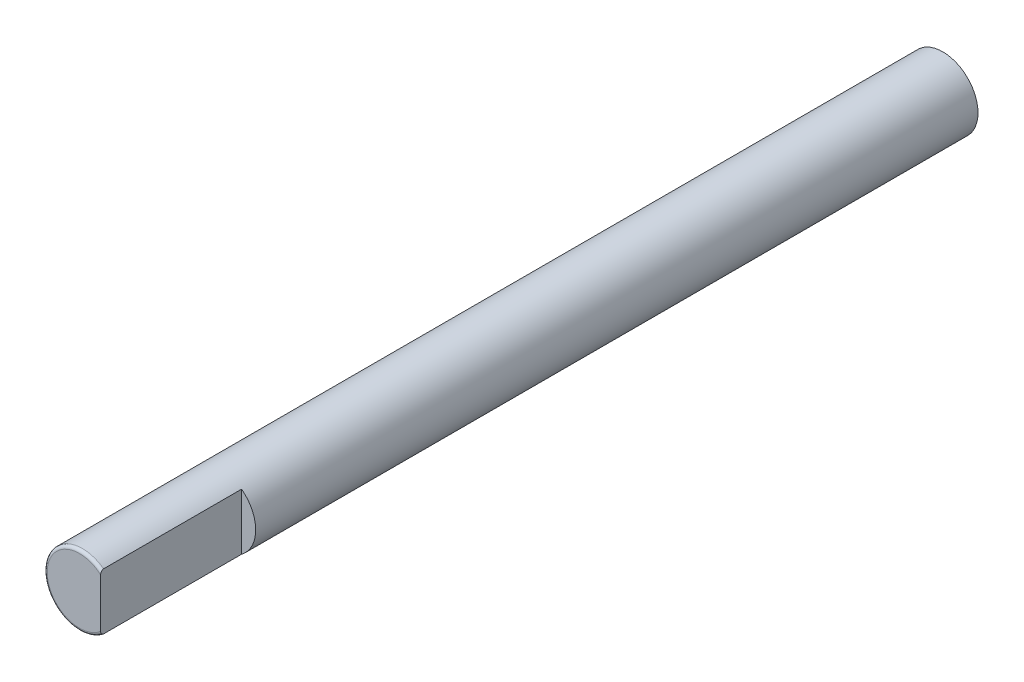
SolidWorks part; units mm, degrees
material "Acero aleado"
ref_plane "Alzado" through (0, 0, 0) normal (0, 0, 1) x (1, 0, 0)
ref_plane "Planta" through (0, 0, 0) normal (0, 1, 0) x (1, 0, 0)
ref_plane "Vista lateral" through (0, 0, 0) normal (1, 0, 0) x (0, 0, -1)
sketch "Croquis1" plane through (0, 0, 0) normal (0, 0, 1) x (1, 0, 0)
  circle A0 centre (0, 0) radius 3
  dimension "D1" = 6
extrude "Saliente-Extruir1" add sketch "Croquis1" along normal blind 73.5
sketch "Croquis2" plane through (0, 0, 73.5) normal (0, 0, 1) x (1, 0, 0)
  circle A0 centre (0, 0) radius 1
  dimension "D1" = 2
fillet "Redondeo1" radius 0.25 1 edges at (3, 0, 73.5)
sketch "Sketch1" plane through (0, 0, 73.5) normal (0, 0, 1) x (1, 0, 0)
  line L1 (1.8, 6.3205) -> (4.8651, 6.3205)
  line L2 (1.8, 6.3205) -> (1.8, -3.6795)
  line L3 (1.8, -3.6795) -> (4.8651, -3.6795)
  line L4 (4.8651, 6.3205) -> (4.8651, -3.6795)
  dimension "D1" = 1.8
  dimension "D2" = 10
extrude "Cut-Extrude1" cut sketch "Sketch1" against normal blind 12
